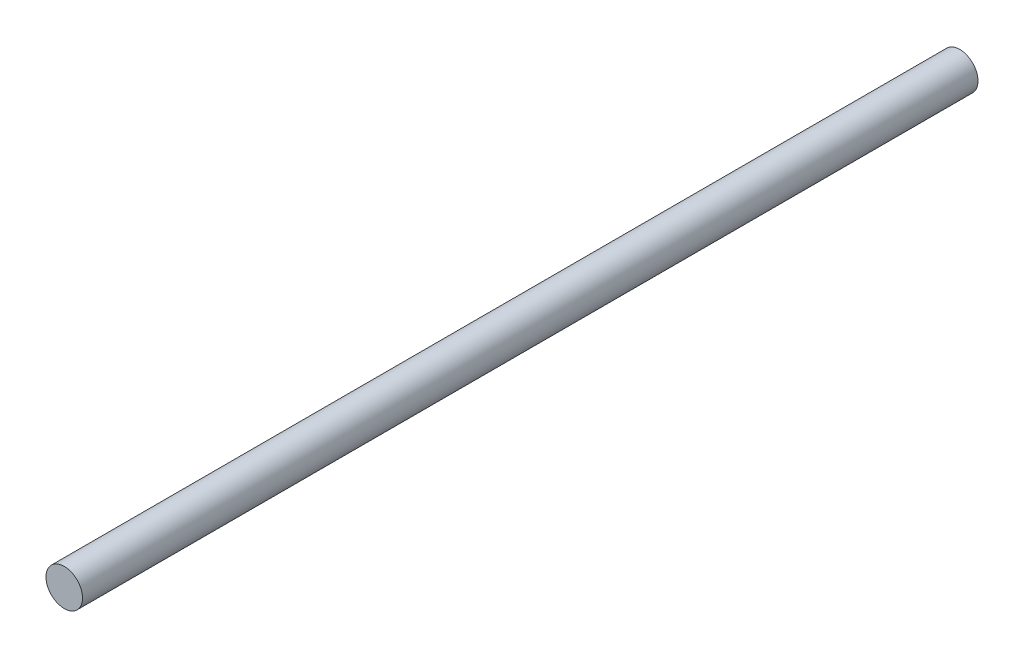
SolidWorks part; units mm, degrees
material "1060 Alloy"
ref_plane "Front Plane" through (0, 0, 0) normal (0, 0, 1) x (1, 0, 0)
ref_plane "Top Plane" through (0, 0, 0) normal (0, 1, 0) x (1, 0, 0)
ref_plane "Right Plane" through (0, 0, 0) normal (1, 0, 0) x (0, 0, -1)
sketch "Sketch1" plane through (0, 0, 0) normal (0, 0, 1) x (1, 0, 0)
  circle A0 centre (0, 0) radius 4
  dimension "D1" = 8
extrude "Boss-Extrude1" add sketch "Sketch1" along normal blind 196
